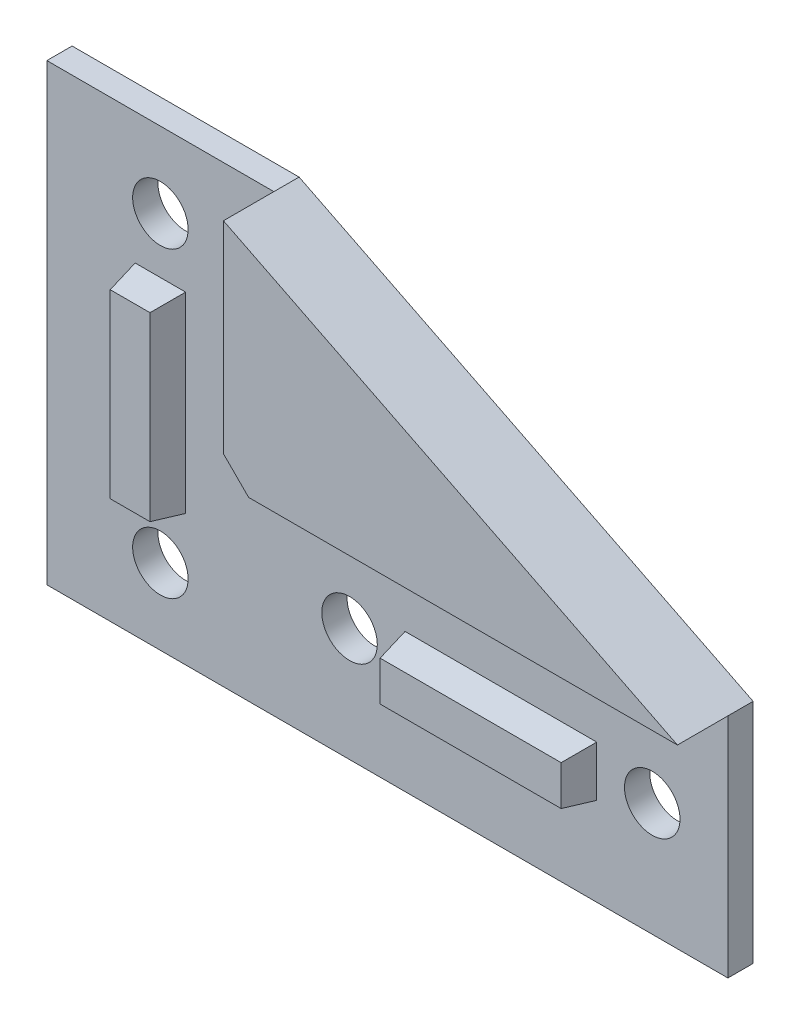
SolidWorks part; units mm, degrees
ref_plane "Plan de face" through (0, 0, 0) normal (0, 0, 1) x (1, 0, 0)
ref_plane "Plan de dessus" through (0, 0, 0) normal (0, 1, 0) x (1, 0, 0)
ref_plane "Plan de droite" through (0, 0, 0) normal (1, 0, 0) x (0, 0, -1)
sketch "Esquisse1" plane through (0, 0, 0) normal (0, 0, 1) x (1, 0, 0)
  line L0 (0, 0) -> (0, 90)
  line L1 (0, 90) -> (45, 90)
  line L2 (45, 90) -> (135, 45)
  line L3 (135, 45) -> (135, 0)
  line L4 (135, 0) -> (0, 0)
  line L5 (22.5, 90) -> (22.5, 22.5) construction
  line L6 (22.5, 22.5) -> (135, 22.5) construction
  circle A1 centre (22.5, 75) radius 5.5
  circle A2 centre (22.5, 15) radius 5.5
  circle A3 centre (120, 22.5) radius 5.5
  circle A4 centre (60, 22.5) radius 5.5
  dimension "D5" = 11
  dimension "D6" = 11
  dimension "D7" = 15
  dimension "D8" = 15
  dimension "D9" = 15
  dimension "D10" = 11
  dimension "D11" = 11
  dimension "D12" = 60
  dimension "D13" = 22.5
  dimension "D1" = 90
  dimension "D2" = 135
  dimension "D3" = 45
  dimension "D4" = 45
extrude "Boss.-Extru.1" add sketch "Esquisse1" along normal blind 5
sketch "Esquisse2" plane through (0, 0, 5) normal (0, 0, 1) x (1, 0, 0)
  line L0 (22.5, 75) -> (22.5, 15) construction
  line L1 (120, 22.5) -> (60, 22.5) construction
  line L3 (17.5, 64) -> (27.5, 64)
  line L4 (17.5, 64) -> (17.5, 26)
  line L5 (17.5, 26) -> (27.5, 26)
  line L6 (27.5, 64) -> (27.5, 26)
  line L7 (71, 27.5) -> (109, 27.5)
  line L8 (71, 27.5) -> (71, 17.5)
  line L9 (71, 17.5) -> (109, 17.5)
  line L10 (109, 27.5) -> (109, 17.5)
  dimension "D1" = 10
  dimension "D2" = 5
  dimension "D3" = 11
  dimension "D4" = 11
  dimension "D5" = 5
  dimension "D6" = 10
  dimension "D7" = 11
  dimension "D8" = 11
extrude "Boss.-Extru.2" add sketch "Esquisse2" along normal blind 6
draft "Dépouille3" type of draft neutral plane draft angle 10 faces to draft 8 face at (90, 27.5, 8) face at (109, 22.5, 8) face at (71, 22.5, 8) face at (90, 17.5, 8) face at (22.5, 26, 8) face at (27.5, 45, 8) face at (22.5, 64, 8) face at (17.5, 45, 8) neutral plane through (0, 0, 5) neutral plane normal (0, 0, 1) parameters "D1"=10
sketch "Esquisse3" plane through (0, 0, 5) normal (0, 0, 1) x (1, 0, 0)
  line L0 (45, 90) -> (45, 45)
  line L1 (45, 45) -> (135, 45)
  line L6 (135, 45) -> (45, 90) construction
  line L7 (45, 90) -> (135, 45)
  circle A0 centre (22.5, 75) radius 5.5 construction
  circle A1 centre (120, 22.5) radius 5.5 construction
  point P5 (55, 90)
  point P6 (55, 55)
  point P7 (135, 55)
  dimension "D1" = 22.5
  dimension "D2" = 22.5
extrude "Boss.-Extru.3" add sketch "Esquisse3" along normal blind 10
chamfer "Chanfrein1" distance 5 angle 45 1 edges at (45, 45, 10)
chamfer "Chanfrein2" [suppressed] distance 5 angle 45
